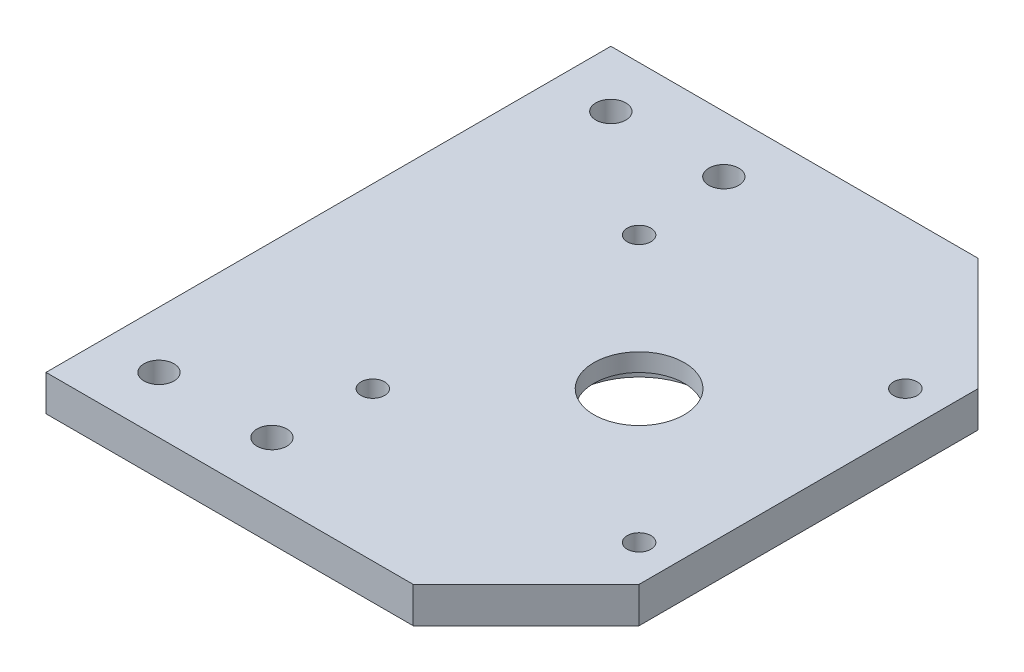
SolidWorks part; units mm, degrees
material "1060 Alloy"
ref_plane "Front Plane" through (0, 0, 0) normal (0, 0, 1) x (1, 0, 0)
ref_plane "Top Plane" through (0, 0, 0) normal (0, 1, 0) x (1, 0, 0)
ref_plane "Right Plane" through (0, 0, 0) normal (1, 0, 0) x (0, 0, -1)
sketch "Sketch1" plane through (0, 0, 0) normal (0, 1, 0) x (1, 0, 0)
  line L0 (0, 0) -> (65, 0)
  line L1 (65, 0) -> (85, -20)
  line L2 (85, -20) -> (85, -80)
  line L3 (85, -80) -> (65, -100)
  line L4 (65, -100) -> (0, -100)
  line L5 (0, -100) -> (0, 0)
  dimension "D1" = 65
  dimension "D2" = 65
  dimension "D3" = 100
  dimension "D4" = 60
  dimension "D5" = 85
  dimension "D6" = 20
extrude "Boss-Extrude1" add sketch "Sketch1" along normal blind 6.35 contours L5 L0 L1 L2 L3 L4
hole_wizard "M5x0.8 Tapped Hole1" positions "Sketch3" profile "Sketch2" tap size "M5x0.8" standard "ANSI Metric" end condition through all
sketch "Sketch3" plane through (0, 6.35, 0) normal (0, 1, 0) x (1, 0, 0)
  line L0 (0, -100) -> (0, 0) construction
  line L1 (0, 0) -> (65, 0) construction
  point P0 (78.57, -26.43)
  point P2 (31.43, -26.43)
  point P4 (31.43, -73.57)
  point P6 (78.57, -73.57)
  dimension "D1" = 47.14
  dimension "D2" = 31.43
  dimension "D3" = 47.14
  dimension "D4" = 26.43
sketch "Sketch2" plane through (78.57, 6.35, 26.43) normal (1, 0, 0) x (0, 0, 1)
  line L0 (0, 0) -> (0, 6.35)
  line L1 (0, 6.35) -> (2.1, 6.35)
  line L2 (2.1, 6.35) -> (2.1, 0)
  line L5 (2.1, 0) -> (0, 0)
  line L11 (0, -6.35) -> (0, 107.95) construction
  dimension "Thru Tap Drill Dia." = 4.2
  dimension "Thru Tap Drill Depth" = 6.35
cosmetic thread "Hole Thread1" parameters "D2"=5
cosmetic thread "Hole Thread2" parameters "D2"=5
cosmetic thread "Hole Thread3" parameters "D2"=5
cosmetic thread "Hole Thread4" parameters "D2"=5
hole_wizard "M5 Clearance Hole1" positions "Sketch5" profile "Sketch4" hole size "M5" standard "ANSI Metric" end condition through all
sketch "Sketch5" plane through (0, 6.35, 0) normal (0, 1, 0) x (1, 0, 0)
  line L0 (0, -100) -> (0, 0) construction
  line L1 (0, 0) -> (65, 0) construction
  line L2 (65, -100) -> (0, -100) construction
  point P0 (10, -10)
  point P2 (30, -10)
  point P4 (10, -90)
  point P6 (30, -90)
  dimension "D1" = 20
  dimension "D2" = 10
  dimension "D3" = 10
  dimension "D4" = 10
sketch "Sketch4" plane through (10, 6.35, 10) normal (1, 0, 0) x (0, 0, 1)
  line L0 (0, 0) -> (0, 6.35)
  line L1 (0, 6.35) -> (2.65, 6.35)
  line L2 (2.65, 6.35) -> (2.65, 0)
  line L5 (2.65, 0) -> (0, 0)
  line L11 (0, -6.35) -> (0, 107.95) construction
  dimension "Thru Hole Dia." = 5.3
  dimension "Thru Hole Depth" = 6.35
sketch "Sketch6" plane through (0, 0, 0) normal (0, 1, 0) x (1, 0, 0)
  circle A0 centre (55, -50) radius 11.5
  circle A1 centre (31.43, -26.43) radius 2.1 construction
  circle A3 centre (31.43, -73.57) radius 2.1 construction
  dimension "D1" = 23.57
  dimension "D2" = 23.57
  dimension "D3" = 23
extrude "Cut-Extrude1" cut sketch "Sketch6" along normal blind 3.175
sketch "Sketch7" plane through (0, 3.175, 0) normal (0, -1, 0) x (-1, 0, 0)
  circle A0 centre (-55, -50) radius 8
  dimension "D1" = 16
extrude "Cut-Extrude2" cut sketch "Sketch7" against normal blind 10
